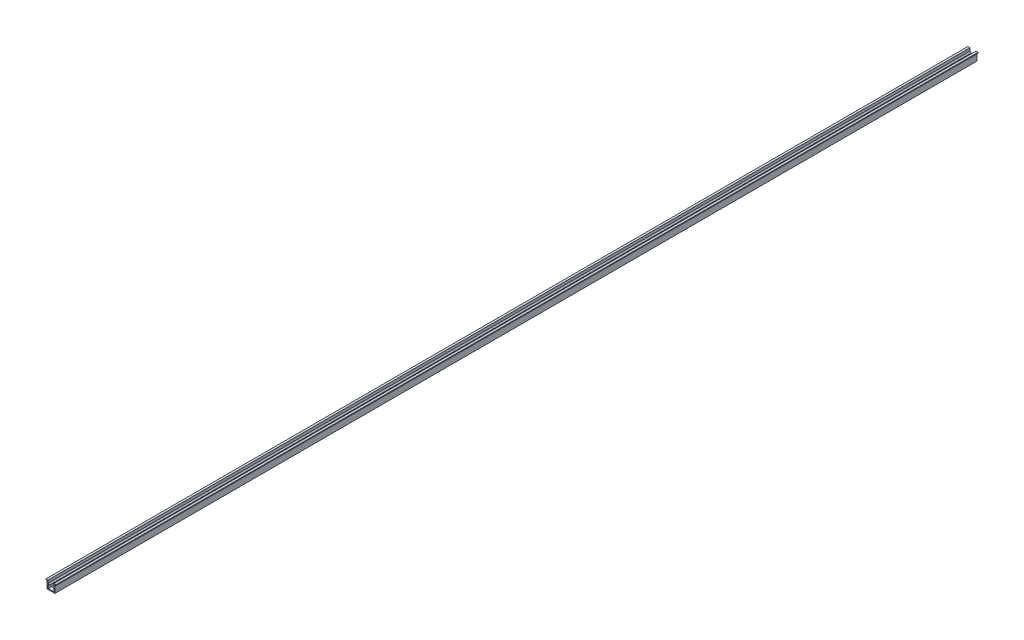
SolidWorks part; units mm, degrees
material "Пластик"
ref_plane "Спереди" through (0, 0, 0) normal (0, 0, 1) x (1, 0, 0)
ref_plane "Сверху" through (0, 0, 0) normal (0, 1, 0) x (1, 0, 0)
ref_plane "Справа" through (0, 0, 0) normal (1, 0, 0) x (0, 0, -1)
sketch "Эскиз1" plane through (0, 0, 0) normal (0, 0, 1) x (1, 0, 0)
  line L0 (4.15, 0) -> (-4.15, 0)
  line L1 (-4.15, 0) -> (-4.15, 8)
  line L2 (-4.15, 8) -> (-5.5, 8)
  line L3 (-5.5, 8) -> (-5.5, 9)
  line L4 (-5.5, 9) -> (-3.15, 9)
  line L5 (-3.15, 9) -> (-3.15, 6)
  line L6 (-3.15, 6) -> (-1.8772, 4.7272)
  line L7 (-1.8772, 4.7272) -> (-2.4429, 4.1615)
  line L8 (-2.4429, 4.1615) -> (-3.15, 4.8686)
  line L9 (-3.15, 4.8686) -> (-3.15, 1)
  line L10 (-3.15, 1) -> (3.15, 1)
  line L11 (0, 1) -> (0, 0) construction
  line L12 (3.15, 4.8686) -> (3.15, 1)
  line L13 (2.4429, 4.1615) -> (3.15, 4.8686)
  line L14 (1.8772, 4.7272) -> (2.4429, 4.1615)
  line L15 (3.15, 6) -> (1.8772, 4.7272)
  line L16 (3.15, 9) -> (3.15, 6)
  line L17 (5.5, 9) -> (3.15, 9)
  line L18 (5.5, 8) -> (5.5, 9)
  line L19 (4.15, 8) -> (5.5, 8)
  line L20 (4.15, 0) -> (4.15, 8)
  line L21 (-4.15, 4) -> (-3.15, 4) construction
  dimension "D1" = 8.3
  dimension "D2" = 11
  dimension "D3" = 6.3
  dimension "D4" = 9
  dimension "D5" = 1
  dimension "D6" = 135
  dimension "D7" = 1.8
  dimension "D8" = 0.8
  dimension "D9" = 3
extrude "Бобышка-Вытянуть1" add sketch "Эскиз1" along normal blind 1000
